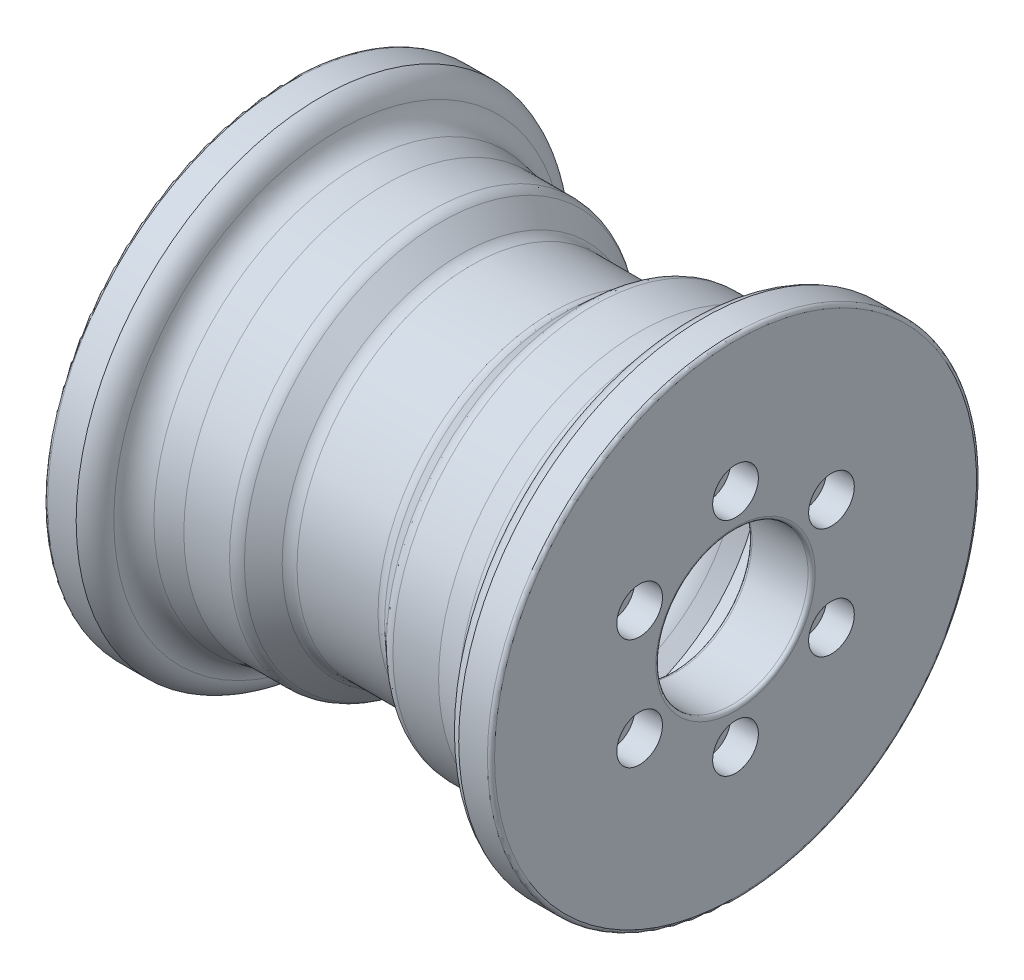
SolidWorks part; units mm, degrees
material "1060 Alloy"
ref_plane "Front Plane" through (0, 0, 0) normal (0, 0, 1) x (1, 0, 0)
ref_plane "Top Plane" through (0, 0, 0) normal (0, 1, 0) x (1, 0, 0)
ref_plane "Right Plane" through (0, 0, 0) normal (1, 0, 0) x (0, 0, -1)
sketch "Sketch1" plane through (0, 0, 0) normal (0, 1, 0) x (1, 0, 0)
  line L0 (0, 0) -> (115.0983, 0) construction
  line L1 (0, 0) -> (0, 307.1864) construction
  line L2 (-91.1401, 122.8618) -> (-76.1379, 120)
  line L3 (-76.1379, 120) -> (-48.8276, 120)
  line L4 (-42.415, 117.5153) -> (-30.6207, 106.7606)
  line L5 (-24.2081, 104.2759) -> (0, 104.2759)
  line L6 (-114.3273, 146.1818) -> (-131.4701, 146.1818)
  line L7 (-133.613, 144.039) -> (-133.613, 47.6601)
  line L8 (-95.7924, 98.474) -> (-78.4848, 95.1724)
  line L9 (-78.4848, 95.1724) -> (-54.76, 95.1724)
  line L10 (-54.76, 95.1724) -> (-47.3493, 88.4149)
  line L11 (-24.2081, 79.4483) -> (0, 79.4483)
  line L12 (-125.0247, 121.3542) -> (-131.4701, 121.3542) construction
  line L13 (-131.4701, 45.5172) -> (-97.9352, 45.5172)
  line L14 (-95.7924, 47.6601) -> (-95.7924, 98.474)
  line L15 (95.7924, 47.6601) -> (95.7924, 98.474)
  line L16 (131.4701, 45.5172) -> (97.9352, 45.5172)
  line L17 (24.2081, 79.4483) -> (0, 79.4483)
  line L18 (54.76, 95.1724) -> (47.3493, 88.4149)
  line L19 (78.4848, 95.1724) -> (54.76, 95.1724)
  line L20 (95.7924, 98.474) -> (78.4848, 95.1724)
  line L21 (133.613, 144.039) -> (133.613, 47.6601)
  line L22 (114.3273, 146.1818) -> (131.4701, 146.1818)
  line L23 (24.2081, 104.2759) -> (0, 104.2759)
  line L24 (42.415, 117.5153) -> (30.6207, 106.7606)
  line L25 (76.1379, 120) -> (48.8276, 120)
  line L26 (91.1401, 122.8618) -> (76.1379, 120)
  arc A0 (-91.1401, 122.8618) -> (-103.456, 134.5612) centre (-88.1965, 138.2927) cw
  arc A1 (-103.456, 134.5612) -> (-114.3273, 146.1818) centre (-119.2241, 130.7053) ccw
  arc A2 (-76.1379, 120) -> (-91.613, 163.9674) centre (-121.6619, 128.6842) ccw construction
  arc A3 (-48.8276, 120) -> (-42.415, 117.5153) centre (-48.8276, 110.4828) cw
  arc A4 (-30.6207, 106.7606) -> (-24.2081, 104.2759) centre (-24.2081, 113.7931) ccw
  arc A5 (-131.4701, 146.1818) -> (-133.613, 144.039) centre (-131.4701, 144.039) ccw
  arc A6 (-133.613, 47.6601) -> (-131.4701, 45.5172) centre (-131.4701, 47.6601) ccw
  arc A7 (-54.76, 95.1724) -> (-54.76, 95.1724) centre (-54.76, 95.1724) cw
  arc A8 (-47.3493, 88.4149) -> (-24.2081, 79.4483) centre (-24.2081, 113.7931) ccw
  arc A9 (-95.7924, 98.474) -> (-125.0247, 121.3542) centre (-88.1965, 138.2927) cw construction
  arc A10 (-125.0247, 121.3542) -> (-125.0247, 121.3542) centre (-125.0247, 121.3542) ccw construction
  arc A11 (-97.9352, 45.5172) -> (-95.7924, 47.6601) centre (-97.9352, 47.6601) ccw
  arc A12 (76.1379, 120) -> (91.613, 163.9674) centre (121.6619, 128.6842) cw construction
  arc A13 (97.9352, 45.5172) -> (95.7924, 47.6601) centre (97.9352, 47.6601) cw
  arc A14 (47.3493, 88.4149) -> (24.2081, 79.4483) centre (24.2081, 113.7931) cw
  arc A15 (133.613, 47.6601) -> (131.4701, 45.5172) centre (131.4701, 47.6601) cw
  arc A16 (131.4701, 146.1818) -> (133.613, 144.039) centre (131.4701, 144.039) cw
  arc A17 (30.6207, 106.7606) -> (24.2081, 104.2759) centre (24.2081, 113.7931) cw
  arc A18 (48.8276, 120) -> (42.415, 117.5153) centre (48.8276, 110.4828) ccw
  arc A19 (103.456, 134.5612) -> (114.3273, 146.1818) centre (119.2241, 130.7053) cw
  arc A20 (91.1401, 122.8618) -> (103.456, 134.5612) centre (88.1965, 138.2927) ccw
  dimension "D4" = 46.3448
  dimension "D6" = 15.7091
  dimension "D7" = 16.2327
  dimension "D11" = 9.5172
  dimension "D16" = 2.1429
  dimension "INNER HEIGHT" = 240
  dimension "D1" = 15.2727
  dimension "D2" = 79.2
  dimension "D3" = 76.1379
  dimension "D5" = 22.7143
  dimension "D8" = 26.1818
  dimension "D9" = 114.3273
  dimension "D10" = 27.3103
  dimension "D12" = 30.6207
  dimension "D13" = 104.2759
  dimension "D14" = 17.1429
  dimension "D17" = 45.5172
  dimension "D15" = 24.8276
revolve "Revolve1" add sketch "Sketch1" angle 360 about L0
hole_wizard "CBORE for M20 SHCS1" positions "Sketch5" profile "Sketch4" counterbore size "M20" standard "ANSI Metric" end condition through all
sketch "Sketch5" plane through (-133.613, 0, 0) normal (-1, 0, 0) x (0, 0, 1)
  point P0 (0, 66.2069)
  dimension "D1" = 66.2069
sketch "Sketch4" plane through (-133.613, 66.2069, 0) normal (0, 1, 0) x (0, 0, 1)
  line L0 (0, 0) -> (0, 267.226)
  line L1 (0, 267.226) -> (9.1034, 267.226)
  line L3 (9.1034, 267.226) -> (9.1034, 16.5517)
  line L4 (9.1034, 16.5517) -> (13.6552, 16.5517)
  line L5 (13.6552, 16.5517) -> (13.6552, 0)
  line L7 (13.6552, 0) -> (0, 0)
  line L11 (0, -6.35) -> (0, 107.95) construction
  dimension "Thru Hole Dia." = 18.2069
  dimension "Thru Hole Depth" = 267.226
  dimension "C'Bore Dia." = 27.3103
  dimension "C'Bore Depth" = 16.5517
pattern_circular "CirPattern1" count 6 over 360 about axis through (0, 0, 0) along (1, 0, 0) of "CBORE for M20 SHCS1"
mirror "Mirror1" about plane through (0, 0, 0) normal (1, 0, 0) of "CirPattern1", "CBORE for M20 SHCS1"
equation "\"D1@Sketch1\"=\"INNER HEIGHT@Sketch1\"*175/2750"
equation "\"D3@Sketch1\"=\"INNER HEIGHT@Sketch1\"*92/290"
equation "\"D4@Sketch1\"=\"INNER HEIGHT@Sketch1\"*56/290"
equation "\"D5@Sketch1\"=\"INNER HEIGHT@Sketch1\"*265/2800"
equation "\"D6@Sketch1\"=\"INNER HEIGHT@Sketch1\"*180/2750"
equation "\"D7@Sketch1\"=\"INNER HEIGHT@Sketch1\"*1860/27500"
equation "\"D8@Sketch1\"=\"INNER HEIGHT@Sketch1\"*300/2750"
equation "\"D9@Sketch1\"=\"INNER HEIGHT@Sketch1\"*131/275"
equation "\"D10@Sketch1\"=\"INNER HEIGHT@Sketch1\"*33/290"
equation "\"D13@Sketch1\"=\"INNER HEIGHT@Sketch1\"*126/290"
equation "\"D12@Sketch1\"=\"INNER HEIGHT@Sketch1\"*37/290"
equation "\"D11@Sketch1\"=\"INNER HEIGHT@Sketch1\"*115/2900"
equation "\"D14@Sketch1\"=\"INNER HEIGHT@Sketch1\"*2/28"
equation "\"D15@Sketch1\"=\"INNER HEIGHT@Sketch1\"*30/290"
equation "\"D16@Sketch1\"=\"INNER HEIGHT@Sketch1\"*25/2800"
equation "\"D17@Sketch1\"=\"INNER HEIGHT@Sketch1\"*55/290"
equation "\"D1@Sketch5\"=\"INNER HEIGHT@Sketch1\"*8/29"
equation "\"Thru Hole Dia.@Sketch4\"=\"INNER HEIGHT@Sketch1\"*22/290"
equation "\"C'Bore Depth@Sketch4\"=\"INNER HEIGHT@Sketch1\"*2/29"
equation "\"C'Bore Dia.@Sketch4\"=\"INNER HEIGHT@Sketch1\"*33/290"
